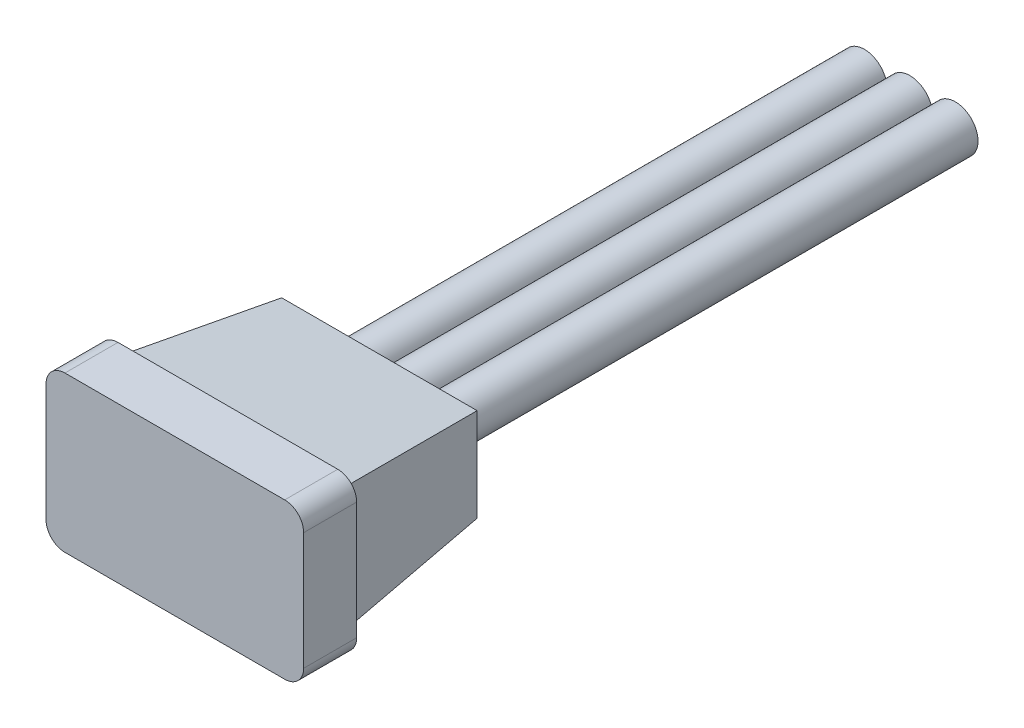
SolidWorks part; units mm, degrees
ref_plane "Front Plane" through (0, 0, 0) normal (0, 0, 1) x (1, 0, 0)
ref_plane "Top Plane" through (0, 0, 0) normal (0, 1, 0) x (1, 0, 0)
ref_plane "Right Plane" through (0, 0, 0) normal (1, 0, 0) x (0, 0, -1)
sketch "Sketch1" plane through (0, 0, 0) normal (0, 0, 1) x (1, 0, 0)
  line L1 (-3.4, 2.05) -> (3.4, 2.05)
  line L2 (-3.4, 2.05) -> (-3.4, -2.05)
  line L3 (-3.4, -2.05) -> (3.4, -2.05)
  line L4 (3.4, 2.05) -> (3.4, -2.05)
  line L5 (-3.4, 2.05) -> (3.4, -2.05) construction
  line L6 (-3.4, -2.05) -> (3.4, 2.05) construction
  point P0 (0, 0)
  dimension "D1" = 6.8
  dimension "D2" = 4.1
extrude "Boss-Extrude1" add sketch "Sketch1" against normal blind 1.4
sketch "Sketch2" plane through (0, 0, -1.4) normal (0, 0, -1) x (-1, 0, 0)
  line L1 (3, 1.65) -> (-3, 1.65)
  line L2 (3, 1.65) -> (3, -1.65)
  line L3 (3, -1.65) -> (-3, -1.65)
  line L4 (-3, 1.65) -> (-3, -1.65)
  line L5 (3, 1.65) -> (-3, -1.65) construction
  line L6 (3, -1.65) -> (-3, 1.65) construction
  line L7 (-3.4, 2.05) -> (3.4, 2.05) construction
  line L8 (-3.4, -2.05) -> (-3.4, 2.05) construction
  point P0 (0, 0)
  dimension "D1" = 0.4
  dimension "D2" = 0.4
extrude "Boss-Extrude2" add sketch "Sketch2" along normal blind 4 draft 6
fillet "Fillet1" radius 0.5 4 edges at (-3.4, -2.05, -0.7) (-3.4, 2.05, -0.7) (3.4, -2.05, -0.7) (3.4, 2.05, -0.7)
sketch "Sketch3" plane through (0, 0, -5.4) normal (0, 0, -1) x (-1, 0, 0)
  circle A0 centre (0, 0) radius 0.6
  dimension "D1" = 1.2
extrude "POSITIVE" add sketch "Sketch3" along normal blind 14 separate body
sketch "Sketch4" plane through (0, 0, -5.4) normal (0, 0, -1) x (-1, 0, 0)
  line L0 (1.2, 0) -> (0, 0) construction
  circle A0 centre (1.2, 0) radius 0.6
  circle A1 centre (0, 0) radius 0.6 construction
extrude "SIGNAL" add sketch "Sketch4" along normal up to surface (14 mm away) separate body up to face at (-0.6, 0, -19.4)
sketch "Sketch5" plane through (0, 0, -5.4) normal (0, 0, -1) x (-1, 0, 0)
  line L0 (0, 0) -> (-1.2, 0) construction
  circle A0 centre (-1.2, 0) radius 0.6
  circle A1 centre (0, 0) radius 0.6 construction
extrude "NEGATIVE" add sketch "Sketch5" along normal up to surface (14 mm away) separate body up to face at (-0.6, 0, -19.4)
